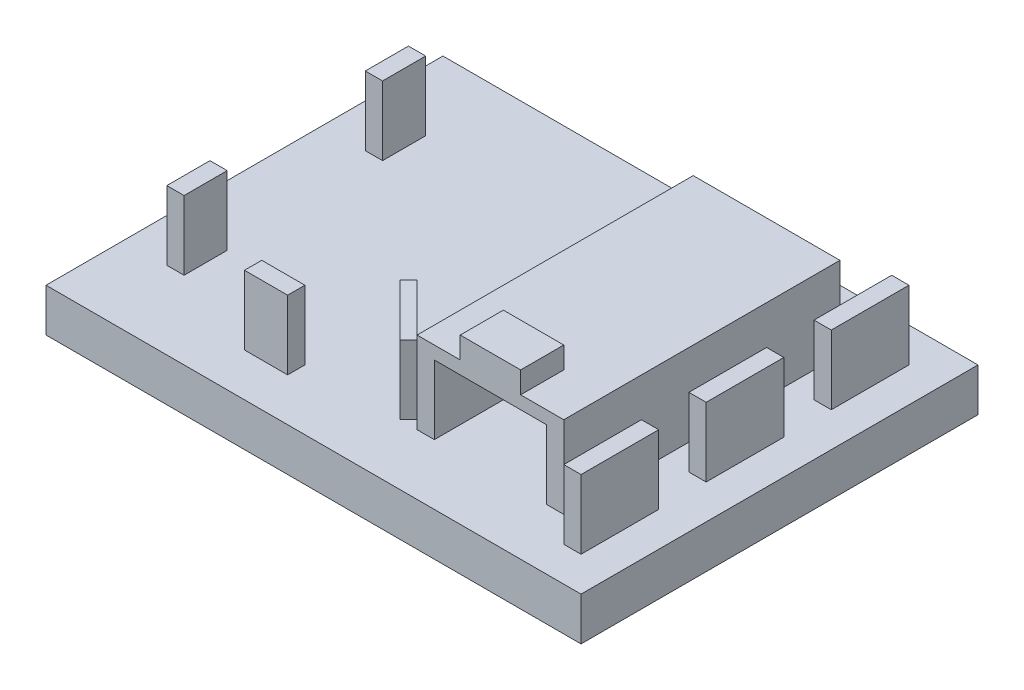
SolidWorks part; units mm, degrees
ref_plane "Front Plane" through (0, 0, 0) normal (0, 0, 1) x (1, 0, 0)
ref_plane "Top Plane" through (0, 0, 0) normal (0, 1, 0) x (1, 0, 0)
ref_plane "Right Plane" through (0, 0, 0) normal (1, 0, 0) x (0, 0, -1)
sketch "Sketch1" plane through (0, 0, 0) normal (0, 1, 0) x (1, 0, 0)
  line L1 (-26.6316, 15.2829) -> (35.3684, 15.2829)
  line L2 (-26.6316, 15.2829) -> (-26.6316, -30.7171)
  line L3 (-26.6316, -30.7171) -> (35.3684, -30.7171)
  line L4 (35.3684, 15.2829) -> (35.3684, -30.7171)
  dimension "D1" = 46
  dimension "D2" = 62
extrude "Boss-Extrude1" add sketch "Sketch1" along normal blind 5
sketch "Sketch2" plane through (0, 5, 0) normal (0, 1, 0) x (1, 0, 0)
  line L0 (35.3684, 15.2829) -> (-26.6316, 15.2829) construction
  line L1 (-21.6316, 6.2829) -> (-19.6316, 6.2829)
  line L2 (-21.6316, 6.2829) -> (-21.6316, 1.2829)
  line L3 (-21.6316, 1.2829) -> (-19.6316, 1.2829)
  line L4 (-19.6316, 6.2829) -> (-19.6316, 1.2829)
  line L5 (-26.6316, -30.7171) -> (35.3684, -30.7171) construction
  line L6 (-19.6316, -16.7171) -> (-21.6316, -16.7171)
  line L7 (-19.6316, -16.7171) -> (-19.6316, -21.7171)
  line L8 (-19.6316, -21.7171) -> (-21.6316, -21.7171)
  line L9 (-21.6316, -16.7171) -> (-21.6316, -21.7171)
  line L10 (-26.6316, 15.2829) -> (-26.6316, -30.7171) construction
  line L11 (7.3684, -23.7171) -> (8.3684, -22.7171)
  line L12 (31.3684, 11.2829) -> (29.3684, 11.2829)
  line L13 (31.3684, 11.2829) -> (31.3684, 2.2829)
  line L14 (31.3684, 2.2829) -> (29.3684, 2.2829)
  line L15 (29.3684, 11.2829) -> (29.3684, 2.2829)
  line L16 (31.3684, -3.2171) -> (29.3684, -3.2171)
  line L17 (31.3684, -3.2171) -> (31.3684, -12.2171)
  line L18 (31.3684, -12.2171) -> (29.3684, -12.2171)
  line L19 (29.3684, -3.2171) -> (29.3684, -12.2171)
  line L20 (31.3684, -17.7171) -> (29.3684, -17.7171)
  line L21 (31.3684, -17.7171) -> (31.3684, -26.7171)
  line L22 (31.3684, -26.7171) -> (29.3684, -26.7171)
  line L23 (29.3684, -17.7171) -> (29.3684, -26.7171)
  line L24 (23.3684, -7.7171) -> (35.3684, -7.7171) construction
  line L25 (35.3684, -30.7171) -> (35.3684, 15.2829) construction
  line L26 (11.3684, 8.2829) -> (9.3684, 8.2829)
  line L27 (26.3684, 8.2829) -> (24.3684, 8.2829)
  line L28 (26.3684, 8.2829) -> (26.3684, -23.7171)
  line L29 (26.3684, -23.7171) -> (24.3684, -23.7171)
  line L30 (24.3684, 8.2829) -> (24.3684, -23.7171)
  line L31 (11.3684, 8.2829) -> (11.3684, -23.7171)
  line L32 (11.3684, -23.7171) -> (9.3684, -23.7171)
  line L33 (9.3684, 8.2829) -> (9.3684, -23.7171)
  line L34 (-8.6316, -23.7171) -> (-3.6316, -23.7171)
  line L35 (-8.6316, -23.7171) -> (-8.6316, -25.7171)
  line L36 (-8.6316, -25.7171) -> (-3.6316, -25.7171)
  line L37 (-3.6316, -23.7171) -> (-3.6316, -25.7171)
  line L38 (8.3684, -22.7171) -> (2.3684, -16.7171)
  line L39 (2.3684, -16.7171) -> (1.3684, -17.7171)
  line L40 (1.3684, -17.7171) -> (7.3684, -23.7171)
  point P26 (29.3684, -7.7171)
  point P31 (29.3684, -7.7171)
  point P44 (1.3684, -17.7171)
  point P45 (2.3684, -16.7171)
  point P46 (7.3684, -23.7171)
  point P47 (8.3684, -22.7171)
  dimension "D1" = 5
  dimension "D2" = 2
  dimension "D3" = 9
  dimension "D4" = 4
  dimension "D5" = 4
  dimension "D6" = 9
  dimension "D7" = 5
  dimension "D8" = 5
  dimension "D9" = 2
  dimension "D10" = 9
  dimension "D11" = 3
  dimension "D12" = 4
  dimension "D13" = 2
  dimension "D14" = 32
  dimension "D15" = 7
  dimension "D16" = 13
  dimension "D17" = 18
  dimension "D18" = 5
  dimension "D22" = 14
  dimension "D23" = 7
  dimension "D24" = 2
  dimension "D25" = 1
  dimension "D26" = 8
extrude "Boss-Extrude2" add sketch "Sketch2" along normal blind 8
sketch "Sketch3" plane through (0, 13, 0) normal (0, 1, 0) x (1, 0, 0)
  line L1 (9.3684, 8.2829) -> (26.3684, 8.2829)
  line L2 (9.3684, 8.2829) -> (9.3684, -23.7171)
  line L3 (9.3684, -23.7171) -> (26.3684, -23.7171)
  line L4 (26.3684, 8.2829) -> (26.3684, -23.7171)
extrude "Boss-Extrude3" add sketch "Sketch3" along normal blind 1.5
sketch "Sketch4" plane through (0, 14.5, 0) normal (0, 1, 0) x (1, 0, 0)
  line L0 (9.3684, -23.7171) -> (26.3684, -23.7171) construction
  line L1 (14.3684, -18.7171) -> (21.3684, -18.7171)
  line L2 (14.3684, -18.7171) -> (14.3684, -23.7171)
  line L3 (14.3684, -23.7171) -> (21.3684, -23.7171)
  line L4 (21.3684, -18.7171) -> (21.3684, -23.7171)
  point P6 (17.8684, -23.7171)
  point P7 (17.8684, -23.7171)
  dimension "D1" = 7
  dimension "D2" = 5
extrude "Boss-Extrude4" add sketch "Sketch4" along normal blind 2.5
